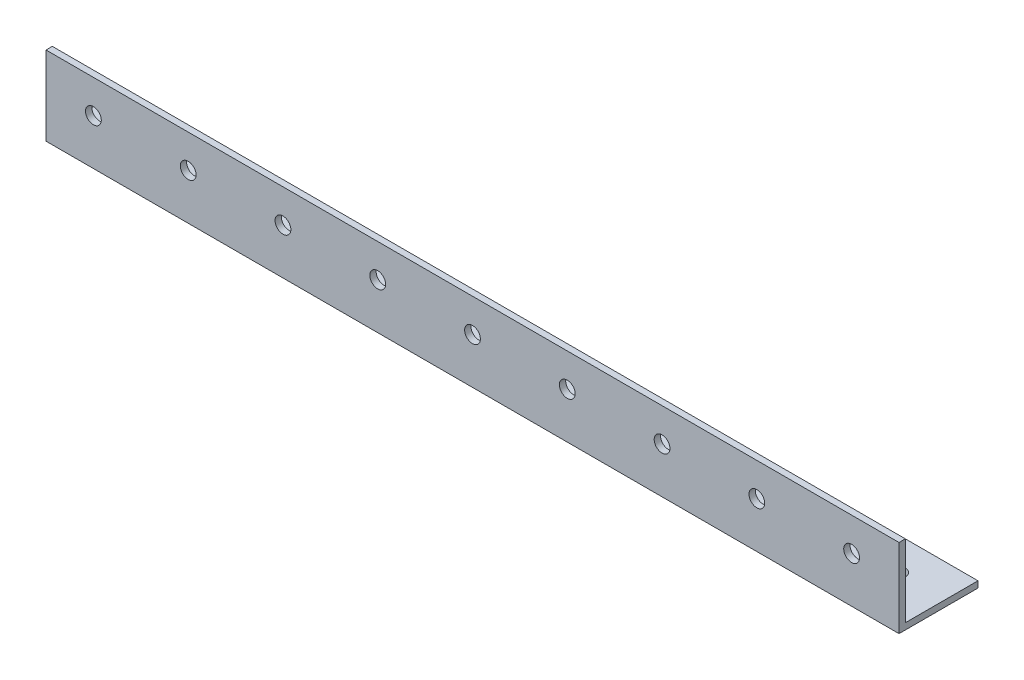
SolidWorks part; units mm, degrees
ref_plane "Спереди" through (0, 0, 0) normal (0, 0, 1) x (1, 0, 0)
ref_plane "Сверху" through (0, 0, 0) normal (0, 1, 0) x (1, 0, 0)
ref_plane "Справа" through (0, 0, 0) normal (1, 0, 0) x (0, 0, -1)
sketch "Эскиз1" plane through (0, 0, 0) normal (1, 0, 0) x (0, 0, -1)
  line L0 (0, 0) -> (0, 50)
  line L1 (0, 0) -> (50, 0)
  dimension "D1" = 50
  dimension "D2" = 50
extrude "Вытянуть-Тонкостенный1" add sketch "Эскиз1" along normal blind 540 thin
sketch "Эскиз2" plane through (0, 0, 0) normal (0, 0, 1) x (1, 0, 0)
  circle A0 centre (30, 29) radius 5
  circle A1 centre (90, 29) radius 5
  circle A2 centre (150, 29) radius 5
  circle A3 centre (210, 29) radius 5
  circle A8 centre (270, 29) radius 5
  circle A29 centre (330, 29) radius 5
  circle A30 centre (390, 29) radius 5
  circle A31 centre (450, 29) radius 5
  circle A32 centre (510, 29) radius 5
  dimension "D1" = 9
extrude "Вырез-Вытянуть1" cut sketch "Эскиз2" against normal through all
sketch "Эскиз3" plane through (0, 0, 0) normal (0, -1, 0) x (1, 0, 0)
  circle A0 centre (30, -29) radius 5
  circle A1 centre (90, -29) radius 5
  circle A2 centre (150, -29) radius 5
  circle A3 centre (210, -29) radius 5
  circle A4 centre (270, -29) radius 5
  circle A5 centre (330, -29) radius 5
  circle A6 centre (390, -29) radius 5
  circle A7 centre (450, -29) radius 5
  circle A8 centre (510, -29) radius 5
  dimension "D1" = 9
extrude "Вырез-Вытянуть2" cut sketch "Эскиз3" against normal through all
